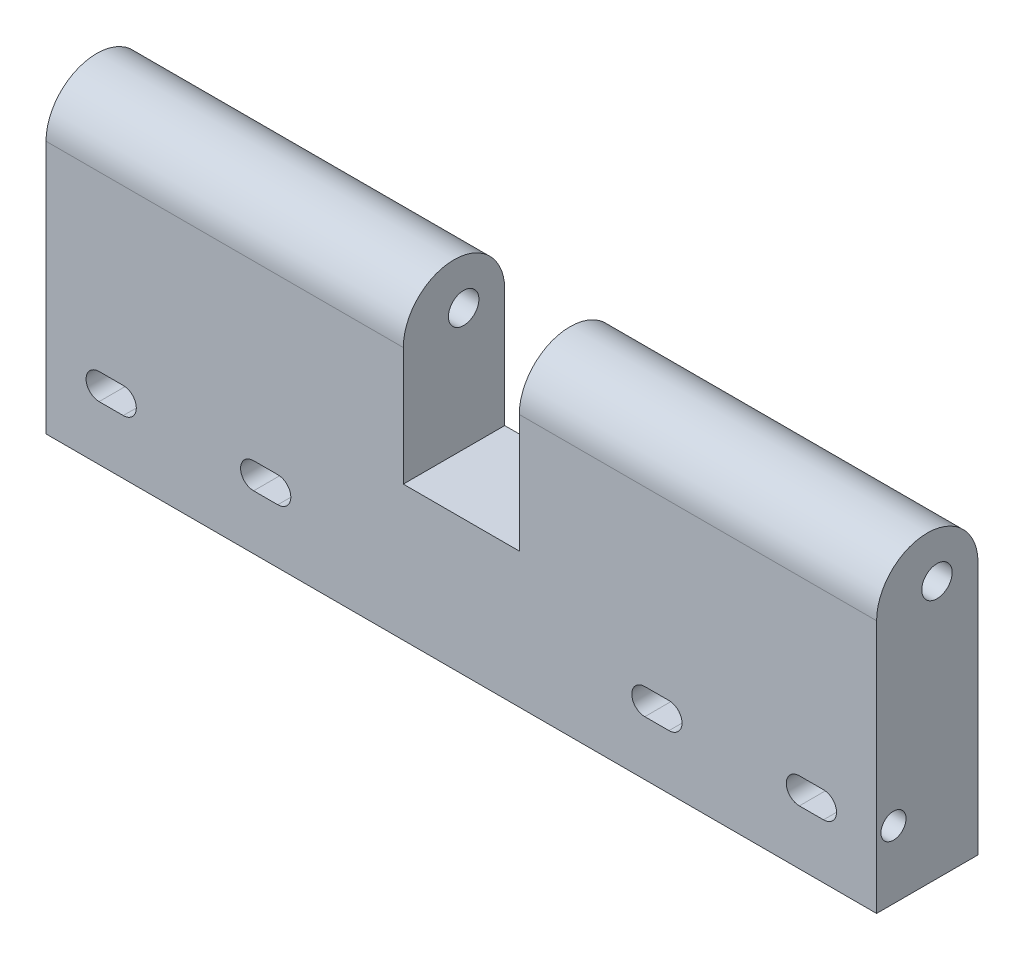
SolidWorks part; units mm, degrees
ref_plane "前视基准面" through (0, 0, 0) normal (0, 0, 1) x (1, 0, 0)
ref_plane "上视基准面" through (0, 0, 0) normal (0, 1, 0) x (1, 0, 0)
ref_plane "右视基准面" through (0, 0, 0) normal (1, 0, 0) x (0, 0, -1)
sketch "草图1" plane through (0, 0, 0) normal (0, 0, 1) x (1, 0, 0)
  line L0 (0, 14) -> (0, -14) construction
  line L1 (86.01, -14) -> (-86.01, -14)
  line L2 (86.01, -14) -> (86.01, 14)
  line L3 (86.01, 14) -> (-86.01, 14)
  line L4 (-86.01, -14) -> (-86.01, 14)
  line L5 (86.01, -14) -> (-86.01, 14) construction
  line L6 (86.01, 14) -> (-86.01, -14) construction
  line L7 (75.01, 0) -> (70.01, 0) construction
  line L8 (75.01, -2.7) -> (70.01, -2.7)
  line L9 (75.01, 2.7) -> (70.01, 2.7)
  line L10 (43.01, 0) -> (38.01, 0) construction
  line L11 (43.01, -2.7) -> (38.01, -2.7)
  line L12 (43.01, 2.7) -> (38.01, 2.7)
  line L13 (-70.01, 0) -> (-75.01, 0) construction
  line L14 (-70.01, -2.7) -> (-75.01, -2.7)
  line L15 (-70.01, 2.7) -> (-75.01, 2.7)
  line L16 (-43.01, 0) -> (-38.01, 0) construction
  line L17 (-43.01, 2.7) -> (-38.01, 2.7)
  line L18 (-43.01, -2.7) -> (-38.01, -2.7)
  arc A4 (75.01, -2.7) -> (75.01, 2.7) centre (75.01, 0) ccw
  arc A5 (70.01, 2.7) -> (70.01, -2.7) centre (70.01, 0) ccw
  arc A6 (43.01, -2.7) -> (43.01, 2.7) centre (43.01, 0) ccw
  arc A7 (38.01, 2.7) -> (38.01, -2.7) centre (38.01, 0) ccw
  arc A8 (-70.01, -2.7) -> (-70.01, 2.7) centre (-70.01, 0) ccw
  arc A9 (-75.01, 2.7) -> (-75.01, -2.7) centre (-75.01, 0) ccw
  arc A10 (-43.01, 2.7) -> (-43.01, -2.7) centre (-43.01, 0) ccw
  arc A11 (-38.01, -2.7) -> (-38.01, 2.7) centre (-38.01, 0) ccw
  point P0 (0, 0)
  point P18 (72.51, 0)
  point P25 (40.51, 0)
  point P30 (-72.51, 0)
  point P37 (-40.51, 0)
  dimension "D8" = 2.7
  dimension "D9" = 2.7
  dimension "D10" = 2.7
  dimension "D11" = 2.7
  dimension "D1" = 172.02
  dimension "D2" = 28
extrude "凸台-拉伸1" add sketch "草图1" along normal blind 21
sketch "草图2" plane through (0, 14, 0) normal (0, 1, 0) x (1, 0, 0)
  line L0 (86.01, 0) -> (-86.01, 0) construction
  line L1 (-86.01, 0) -> (-12.01, 0)
  line L2 (-86.01, 0) -> (-86.01, -21)
  line L3 (-86.01, -21) -> (-12.01, -21)
  line L4 (-12.01, 0) -> (-12.01, -21)
  line L5 (86.01, -21) -> (-86.01, -21) construction
  line L6 (86.01, -21) -> (86.01, 0) construction
  line L7 (86.01, 0) -> (12.01, 0)
  line L8 (86.01, 0) -> (86.01, -21)
  line L9 (86.01, -21) -> (12.01, -21)
  line L10 (12.01, 0) -> (12.01, -21)
  dimension "D1" = 74
  dimension "D2" = 74
extrude "凸台-拉伸2" add sketch "草图2" along normal blind 35
sketch "草图3" plane through (86.01, 0, 0) normal (1, 0, 0) x (0, 0, -1)
  line L0 (-21, 49) -> (0, 49) construction
  line L1 (-21, -14) -> (-21, 49) construction
  line L2 (-21, 49) -> (0, 49)
  line L3 (-21, 49) -> (-21, 38.5)
  line L4 (-21, 38.5) -> (0, 38.5)
  line L5 (0, 49) -> (0, 38.5)
  circle A0 centre (-10.5, 38.5) radius 10.5
  line M5 (0, -14) -> (0, 49)
  line M6 (0, 49) -> (-21, 49)
  line M7 (-21, 49) -> (-21, -14)
  dimension "D1" = 10.5
  dimension "D2" = 21
  dimension "D3" = 10.5
extrude "切除-拉伸1" cut sketch "草图3" against normal through all contours A0 M5 M6 | A0 L2 M7
sketch "草图4" plane through (86.01, 0, 0) normal (1, 0, 0) x (0, 0, -1)
  circle A0 centre (-8.5002, 39.35) radius 3.15
  dimension "D1" = 6.3
extrude "切除-拉伸2" cut sketch "草图4" against normal through all
sketch "草图6" plane through (86.01, 0, 0) normal (1, 0, 0) x (0, 0, -1)
  circle A0 centre (-17.5, 0) radius 2.6
  dimension "D1" = 5.2
extrude "切除-拉伸3" cut sketch "草图6" against normal blind 8
sketch "草图7" plane through (-86.01, 0, 0) normal (-1, 0, 0) x (0, 0, 1)
  circle A0 centre (17.5, 0) radius 2.6
  dimension "D1" = 5.2
extrude "切除-拉伸4" cut sketch "草图7" against normal blind 8
